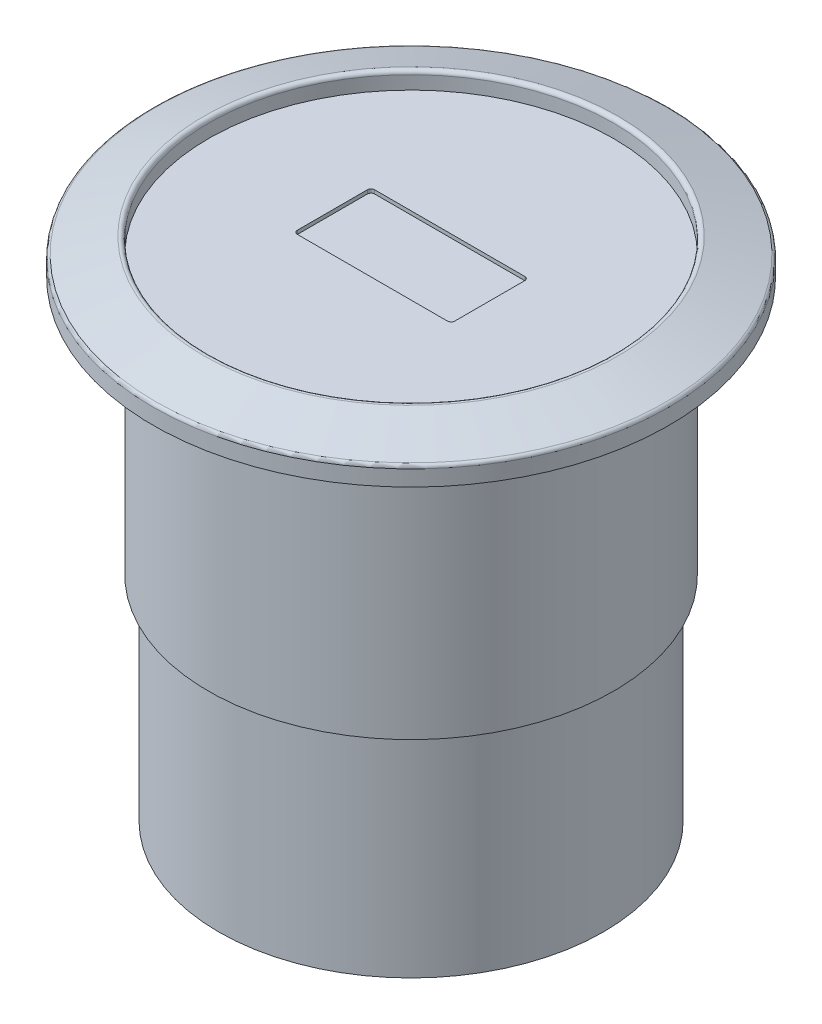
SolidWorks part; units mm, degrees
material "6061 Alloy"
ref_plane "Front Plane" through (0, 0, 0) normal (0, 0, 1) x (1, 0, 0)
ref_plane "Top Plane" through (0, 0, 0) normal (0, 1, 0) x (1, 0, 0)
ref_plane "Right Plane" through (0, 0, 0) normal (1, 0, 0) x (0, 0, -1)
sketch "Sketch1" plane through (0, 0, 0) normal (0, 0, 1) x (1, 0, 0)
  line L0 (0, 0) -> (0, 27.6) construction
  line L1 (0, 27.6) -> (-11, 27.6) construction
  line L2 (-11, 27.6) -> (-14, 26.6)
  line L3 (-14, 26.6) -> (-14, 25.6)
  line L4 (-14, 25.6) -> (-11, 25.6)
  line L5 (-11, 25.6) -> (-11, 11.6)
  line L6 (-11, 11.6) -> (-10.45, 11.6)
  line L7 (-10.45, 11.6) -> (-10.45, 0)
  line L8 (-10.45, 0) -> (0, 0)
  line L9 (-11, 25.6) -> (-11, 27.6) construction
  line L10 (0, 0) -> (0, 26.6)
  line L11 (0, 26.6) -> (-11, 26.6)
  line L12 (-11, 26.6) -> (-11, 27.6)
  line L13 (-11, 26.6) -> (-14, 26.6) construction
  dimension "D1" = 11
  dimension "D2" = 10.45
  dimension "D3" = 25.6
  dimension "D4" = 2
  dimension "D5" = 14
  dimension "D6" = 11.6
  dimension "D8" = 1
revolve "Revolve1" add sketch "Sketch1" angle 360 about L10
cosmetic thread "Cosmetic Thread1" parameters "D2"=20.92
fillet "Fillet1" radius 0.2 2 edges at (0, 26.6, -14) (0, 27.6, -11)
sketch "Sketch2" plane through (0, 26.6, 0) normal (0, 1, 0) x (1, 0, 0)
  line L1 (-4.275, -2.1) -> (4.275, -2.1)
  line L2 (-4.275, -2.1) -> (-4.275, 2.1)
  line L3 (-4.275, 2.1) -> (4.275, 2.1)
  line L4 (4.275, -2.1) -> (4.275, 2.1)
  line L5 (-4.275, -2.1) -> (4.275, 2.1) construction
  line L6 (-4.275, 2.1) -> (4.275, -2.1) construction
  point P0 (0, 0)
  dimension "D1" = 8.55
  dimension "D2" = 4.2
extrude "Cut-Extrude1" cut sketch "Sketch2" against normal blind 0.2 contours L2 L3 L4 L1
fillet "Fillet2" radius 0.2 4 edges at (4.275, 26.5, -2.1) (4.275, 26.5, 2.1) (-4.275, 26.5, 2.1) (-4.275, 26.5, -2.1)
